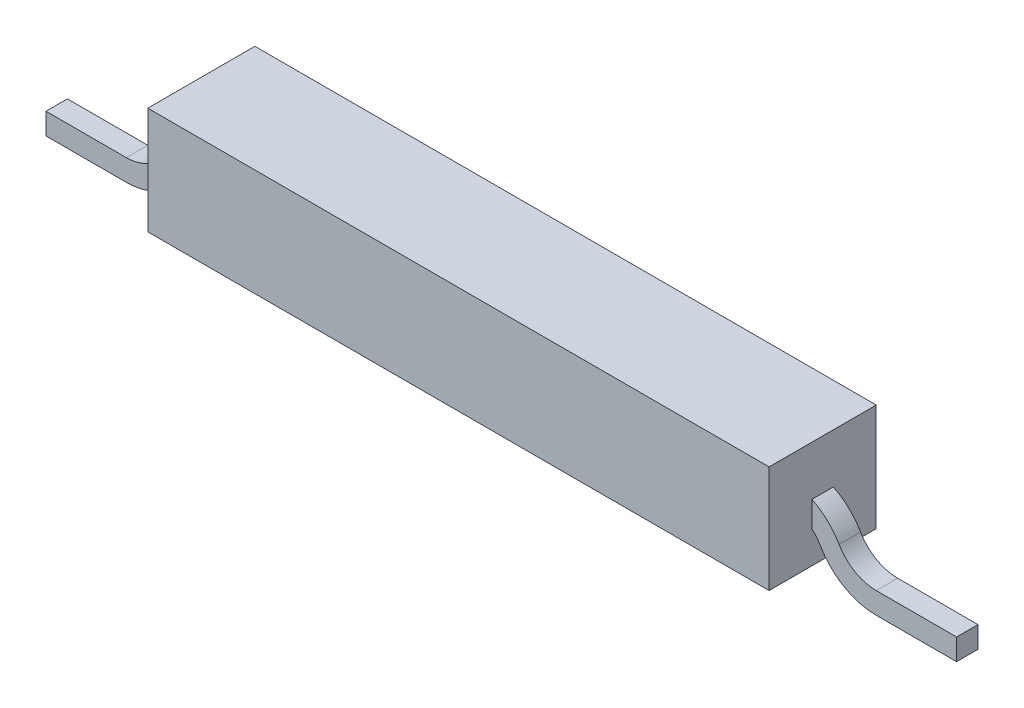
SolidWorks part; units mm, degrees
ref_plane "Plan de face" through (0, 0, 0) normal (0, 0, 1) x (1, 0, 0)
ref_plane "Plan de dessus" through (0, 0, 0) normal (0, 1, 0) x (1, 0, 0)
ref_plane "Plan de droite" through (0, 0, 0) normal (1, 0, 0) x (0, 0, -1)
sketch "Esquisse2" plane through (0, 0, 0) normal (0, 0, 1) x (1, 0, 0)
  line L0 (5.2679, 0) -> (-5.2679, 0)
  line L1 (-7, -1) -> (-8.5, -1)
  line L2 (0, 0) -> (0, -0.7008) construction
  line L3 (7, -1) -> (8.5, -1)
  arc A0 (-5.2679, 0) -> (-6.134, -0.5) centre (-5.2679, -1) ccw
  arc A1 (-6.134, -0.5) -> (-7, -1) centre (-7, 0) cw
  arc A2 (6.134, -0.5) -> (7, -1) centre (7, 0) ccw
  arc A3 (5.2679, 0) -> (6.134, -0.5) centre (5.2679, -1) cw
  dimension "D3" = 1.5
  dimension "D1" = 8.5
  dimension "D2" = 1
sketch "Esquisse6" plane through (0, 0, 0) normal (1, 0, 0) x (0, 0, -1)
  line L1 (-1, -1) -> (1, -1)
  line L2 (-1, -1) -> (-1, 1)
  line L3 (-1, 1) -> (1, 1)
  line L4 (1, -1) -> (1, 1)
  line L5 (-1, -1) -> (1, 1) construction
  line L6 (-1, 1) -> (1, -1) construction
  point P0 (0, 0)
  dimension "D1" = 2
extrude "Boss.-Extru.3" add sketch "Esquisse6" along normal mid plane 11.6
ref_plane "Plan1" through (8.5, 0, 0) normal (1, 0, 0) x (0, 0, -1)
sketch "Esquisse7" plane through (8.5, 0, 0) normal (1, 0, 0) x (0, 0, -1)
  line L1 (0.2, -0.8) -> (-0.2, -0.8)
  line L2 (0.2, -0.8) -> (0.2, -1.2)
  line L3 (0.2, -1.2) -> (-0.2, -1.2)
  line L4 (-0.2, -0.8) -> (-0.2, -1.2)
  line L5 (0.2, -0.8) -> (-0.2, -1.2) construction
  line L6 (0.2, -1.2) -> (-0.2, -0.8) construction
  point P0 (0, -1)
  dimension "D1" = 0.4
sweep "Balayage1" add profiles "Esquisse7" path "Esquisse2"
